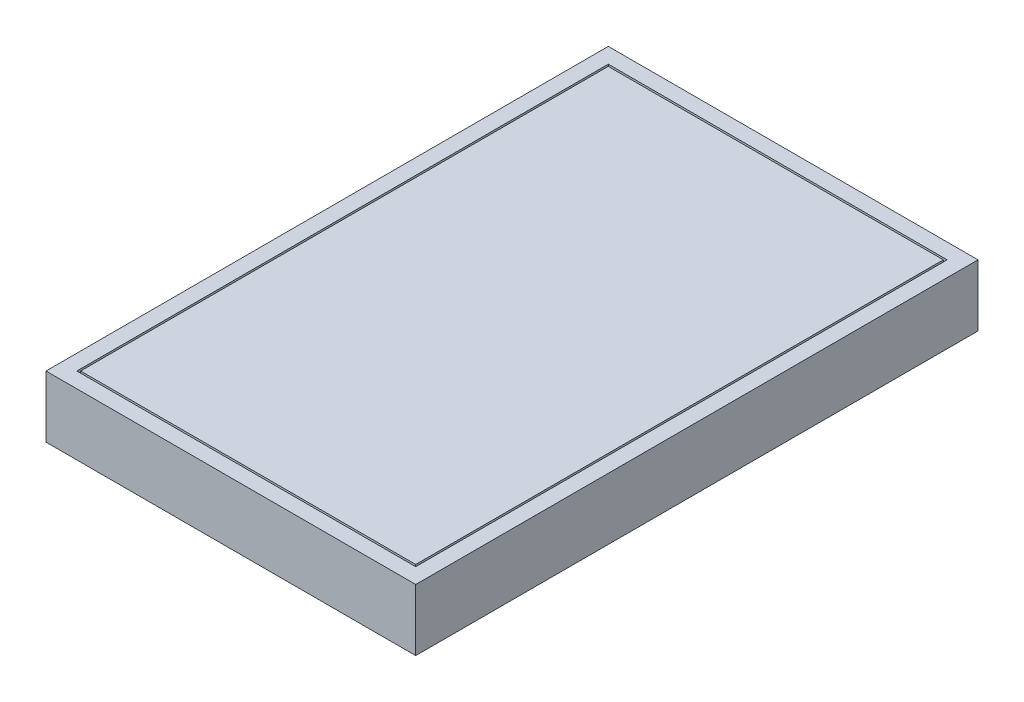
SolidWorks part; units mm, degrees
ref_plane "Front Plane" through (0, 0, 0) normal (0, 0, 1) x (1, 0, 0)
ref_plane "Top Plane" through (0, 0, 0) normal (0, 1, 0) x (1, 0, 0)
ref_plane "Right Plane" through (0, 0, 0) normal (1, 0, 0) x (0, 0, -1)
ref_plane "Plane1" through (0, -60, 0) normal (0, -1, 0) x (1, 0, 0)
sketch "Sketch1" plane through (0, -60, 0) normal (0, -1, 0) x (1, 0, 0)
  line L0 (-240, 0) -> (240, 0)
  line L1 (240, 0) -> (240, 730)
  line L2 (240, 730) -> (-240, 730)
  line L3 (-240, 730) -> (-240, 0)
  dimension "D1" = 730
  dimension "D2" = 240
  dimension "D3" = 480
extrude "Boss-Extrude1" add sketch "Sketch1" against normal blind 80
sketch "Sketch2" plane through (0, 20, 0) normal (0, 1, 0) x (-1, 0, 0)
  line L0 (220, 710) -> (-220, 710)
  line L1 (-220, 710) -> (-220, 20)
  line L2 (-220, 20) -> (220, 20)
  line L3 (220, 20) -> (220, 710)
  dimension "D1" = 20
  dimension "D2" = 690
  dimension "D3" = 220
  dimension "D4" = 440
extrude "Cut-Extrude1" cut sketch "Sketch2" against normal blind 11
sketch "Sketch3" plane through (0, 9, 0) normal (0, 1, 0) x (-1, 0, 0)
  line L0 (217.5, 707.5) -> (217.5, 22.5)
  line L1 (217.5, 22.5) -> (-217.5, 22.5)
  line L2 (-217.5, 22.5) -> (-217.5, 707.5)
  line L3 (-217.5, 707.5) -> (217.5, 707.5)
  line L4 (-220, 20) -> (220, 20) construction
  line L5 (220, 20) -> (220, 710) construction
  dimension "D1" = 2.5
  dimension "D2" = 685
  dimension "D3" = 2.5
  dimension "D4" = 435
extrude "Boss-Extrude2" add sketch "Sketch3" along normal blind 11
